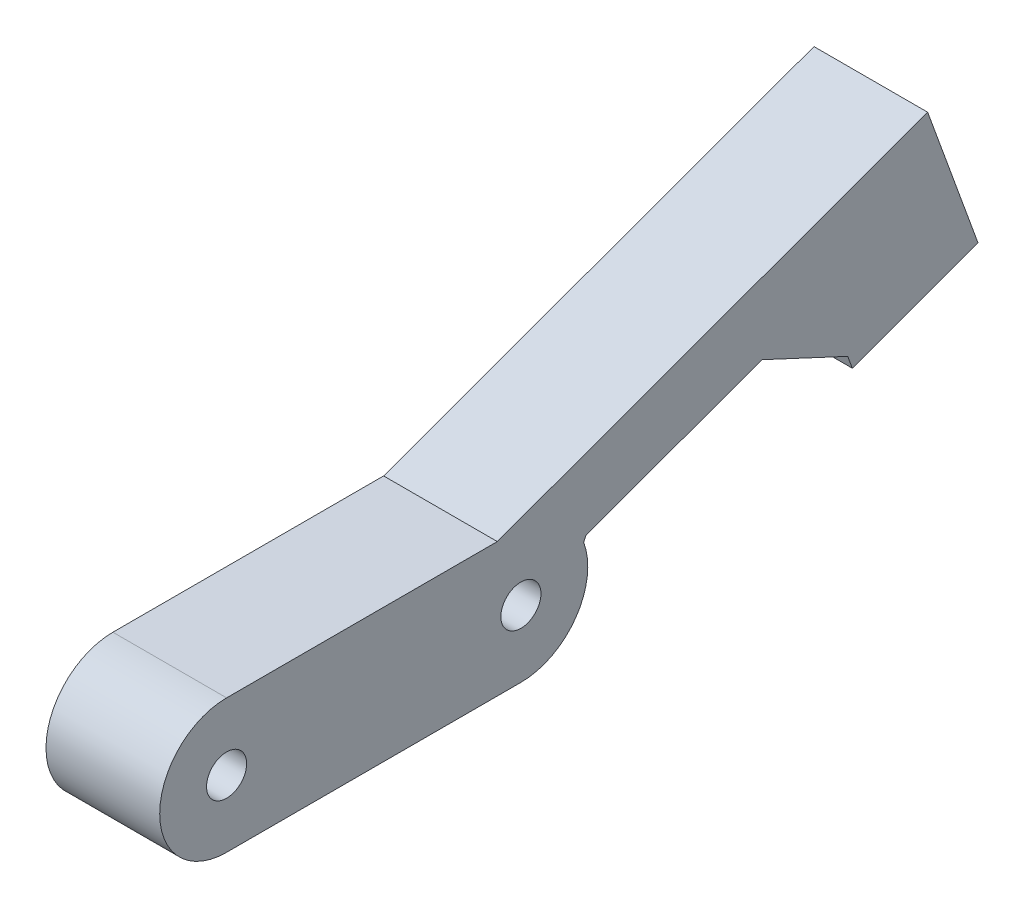
SolidWorks part; units mm, degrees
ref_plane "Front Plane" through (0, 0, 0) normal (0, 0, 1) x (1, 0, 0)
ref_plane "Top Plane" through (0, 0, 0) normal (0, 1, 0) x (1, 0, 0)
ref_plane "Right Plane" through (0, 0, 0) normal (1, 0, 0) x (0, 0, -1)
sketch "Sketch1" plane through (0, 0, 0) normal (1, 0, 0) x (0, 0, -1)
  line L1 (0, 0) -> (27, 0)
  line L2 (0, 0) -> (0, 10)
  line L3 (0, 10) -> (27, 10)
  circle A0 centre (5, 5) radius 1.5
  circle A1 centre (5, 5) radius 5
  circle A2 centre (27, 5) radius 5
  circle A3 centre (27, 5) radius 1.5
  dimension "D7" = 3
  dimension "D11" = 10
  dimension "D2" = 3
  dimension "D1" = 10
  dimension "D8" = 5
  dimension "D9" = 5
  dimension "D10" = 22
extrude "Boss-Extrude1" add sketch "Sketch1" along normal blind 8.5 contours A1 A0 | A2 L3 A1 L1 | A2 A3 | L2 A1 | L1 A1
sketch "Sketch2" plane through (8.5, 0, 0) normal (1, 0, 0) x (0, 0, -1)
  line L0 (27, 0) -> (60.8289, 12.3127)
  line L1 (5, 0) -> (27, 0) construction
  line L3 (60.8289, 12.3127) -> (57.4087, 21.7097)
  line L5 (57.4087, 21.7097) -> (25.2367, 10)
  line L6 (5, 10) -> (27, 10) construction
  line L7 (31.8677, 7.0926) -> (45.0234, 11.8809)
  line L8 (31.8677, 7.0926) -> (28.8794, 0.684)
  line L9 (45.0234, 11.8809) -> (51.432, 8.8925)
  line L10 (51.432, 8.8925) -> (60.8289, 12.3127)
  line L11 (51.432, 8.8925) -> (51.774, 7.9528)
  line L12 (60.8289, 12.3127) -> (61.171, 11.373)
  line L13 (51.774, 7.9528) -> (61.171, 11.373)
  line L14 (5, 10) -> (27, 10)
  arc A3 (27, 0) -> (27, 10) centre (27, 5) ccw construction
  arc A4 (27, 0) -> (27, 10) centre (27, 5) ccw
  line M1 (27, 10) -> (5, 10)
  arc M4 (27, 0) -> (27, 10) centre (27, 5) ccw
  dimension "D1" = 160
  dimension "D2" = 36
  dimension "D3" = 90
  dimension "D4" = 10
  dimension "D5" = 10
  dimension "D6" = 45
  dimension "D7" = 45
  dimension "D8" = 5
  dimension "D9" = 5
  dimension "D10" = 14
  dimension "D11" = 1
extrude "Boss-Extrude2" add sketch "Sketch2" against normal blind 8.5 contours L7 L9 L0 L3 L5 L8 M1 M4 | L11 L13 L12 L0
sketch "Sketch3" plane through (8.5, 0, 0) normal (1, 0, 0) x (0, 0, -1)
  line L0 (51.432, 8.8925) -> (27, 0)
  line L1 (5, 0) -> (27, 0) construction
  circle A0 centre (27, 5) radius 5
  arc M4 (27, 0) -> (31.6945, 6.721) centre (27, 5) ccw
  dimension "D1" = 160
extrude "Cut-Extrude1" [suppressed] cut sketch "Sketch3" against normal blind 3 contours L0 M4
sketch "Sketch4" plane through (8.5, 0, 0) normal (1, 0, 0) x (0, 0, -1)
  line L0 (52.2404, 19.8285) -> (59.2898, 16.5413)
  line L1 (57.4087, 21.7097) -> (25.2367, 10) construction
  line L2 (61.171, 11.373) -> (57.4087, 21.7097) construction
  line L3 (45.0234, 11.8809) -> (51.432, 8.8925) construction
  line L4 (57.4087, 21.7097) -> (25.2367, 10)
  line L5 (61.171, 11.373) -> (57.4087, 21.7097)
  line M8 (61.171, 11.373) -> (57.4087, 21.7097)
  line M9 (57.4087, 21.7097) -> (25.2367, 10)
extrude "Cut-Extrude2" [suppressed] cut sketch "Sketch4" against normal through all contours L0 M9 M8
